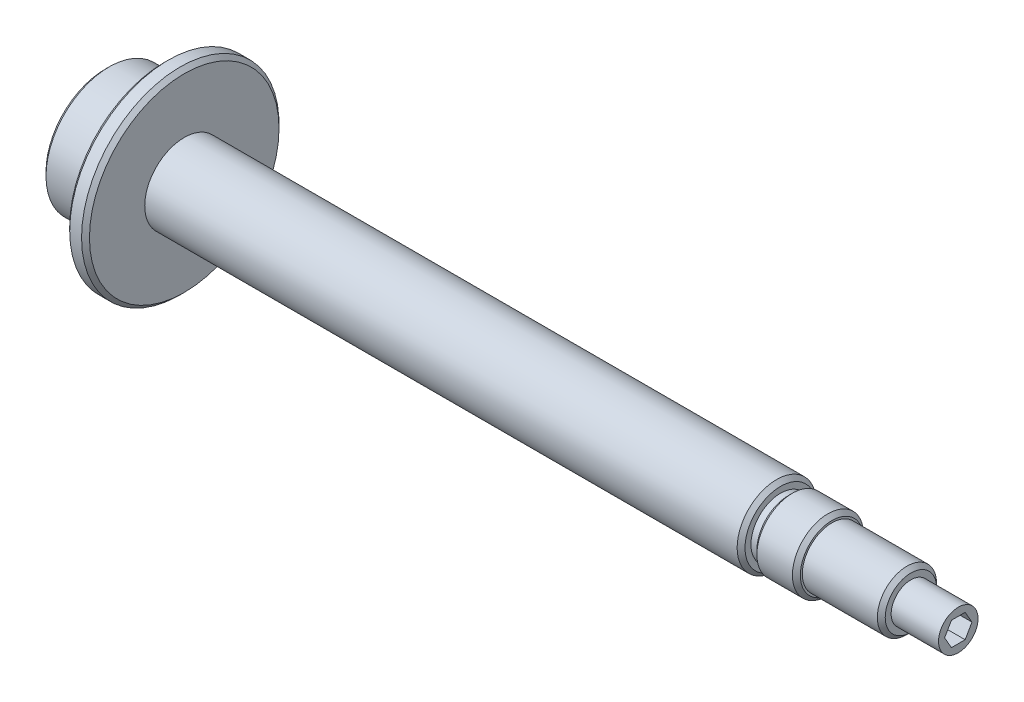
SolidWorks part; units mm, degrees
ref_plane "Спереди" through (0, 0, 0) normal (0, 0, 1) x (1, 0, 0)
ref_plane "Сверху" through (0, 0, 0) normal (0, 1, 0) x (1, 0, 0)
ref_plane "Справа" through (0, 0, 0) normal (1, 0, 0) x (0, 0, -1)
other "Configuration Table"
sketch "Эскиз1" plane through (0, 0, 0) normal (0, 0, 1) x (1, 0, 0)
  line L0 (0, 0) -> (0, 15)
  line L1 (1, 16) -> (15, 16)
  line L2 (15, 16) -> (15, 24)
  line L3 (16, 25) -> (19, 25)
  line L4 (20, 24) -> (20, 10)
  line L5 (20, 10) -> (170, 10)
  line L7 (174, 9) -> (183, 9)
  line L8 (184, 8) -> (184, 7.5)
  line L9 (184, 7.5) -> (203, 7.5)
  line L10 (204, 6.5) -> (204, 5)
  line L11 (204, 5) -> (216, 5)
  line L12 (216, 4) -> (216, 0)
  line L14 (0, 0) -> (225.6844, 0) construction
  line L15 (0, 0) -> (216, 0)
  line L16 (171, 9) -> (171, 7.5)
  line L17 (171, 7.5) -> (173, 7.5)
  line L18 (173, 7.5) -> (173, 8)
  line L19 (170, 10) -> (171, 9)
  line L20 (173, 8) -> (174, 9)
  line L21 (183, 9) -> (184, 8)
  line L22 (203, 7.5) -> (204, 6.5)
  line L23 (216, 5) -> (216, 4)
  line L24 (15, 24) -> (16, 25)
  line L25 (0, 15) -> (1, 16)
  line L26 (19, 25) -> (20, 24)
  point P1 (0, 16)
  point P5 (15, 25)
  point P6 (20, 25)
  point P10 (184, 9)
  point P12 (204, 7.5)
  point P14 (216, 5)
  point P17 (171, 10)
  point P21 (173, 9)
  dimension "D1" = 32
  dimension "D2" = 50
  dimension "D3" = 15
  dimension "D4" = 5
  dimension "D5" = 20
  dimension "D6" = 18
  dimension "D7" = 15
  dimension "D8" = 12
  dimension "D9" = 151
  dimension "D10" = 2
  dimension "D11" = 20
  dimension "D12" = 10
  dimension "D13" = 15
  dimension "D14" = 11
revolve "Повернуть1" add sketch "Эскиз1" angle 360 about L14
cosmetic thread "Условное изображение резьбы2" parameters "D2"=15.252
cosmetic thread "Условное изображение резьбы3" parameters "D1"=5, "D2"=8.344
hole_wizard "Отверстие обработанное метчиком M101" positions "Эскиз4" profile "Эскиз3" tap size "M10" standard "DIN"
sketch "Эскиз4" plane through (0, 0, 0) normal (-1, 0, 0) x (0, 0, 1)
  point P0 (0, 0)
sketch "Эскиз3" plane through (0, 0, 0) normal (0, 1, 0) x (0, 0, 1)
  line L0 (0, 0) -> (0, 27.5)
  line L1 (0, 27.5) -> (4.25, 24.9463)
  line L2 (4.25, 24.9463) -> (4.25, 0.775)
  line L3 (4.25, 0.775) -> (5.025, 0)
  line L5 (5.025, 0) -> (0, 0)
  line L6 (-4.25, 0.775) -> (-5.025, 0) construction
  line L10 (0, 27.5) -> (-4.25, 24.9463) construction
  line L11 (0, -6.35) -> (0, 107.95) construction
  dimension "Диаметр сверла" = 8.5
  dimension "Глубина сверла" = 27.5
  dimension "Диаметр передней зенковки" = 10.05
  dimension "Угол передней зенковки" = 90
  dimension "Угол заточки сверла" = 118
cosmetic thread "Отверстие резьбы1" parameters "D1"=20, "D2"=10
sketch "Эскиз5" plane through (216, 0, 0) normal (1, 0, 0) x (0, 0, -1)
  line L1 (3.4641, 0) -> (1.7321, 3)
  line L2 (1.7321, 3) -> (-1.7321, 3)
  line L3 (-1.7321, 3) -> (-3.4641, 0)
  line L4 (-3.4641, 0) -> (-1.7321, -3)
  line L5 (-1.7321, -3) -> (1.7321, -3)
  line L6 (1.7321, -3) -> (3.4641, 0)
  circle A0 centre (0, 0) radius 3 construction
  dimension "D1" = 6
extrude "Вырез-Вытянуть1" cut sketch "Эскиз5" against normal blind 15
